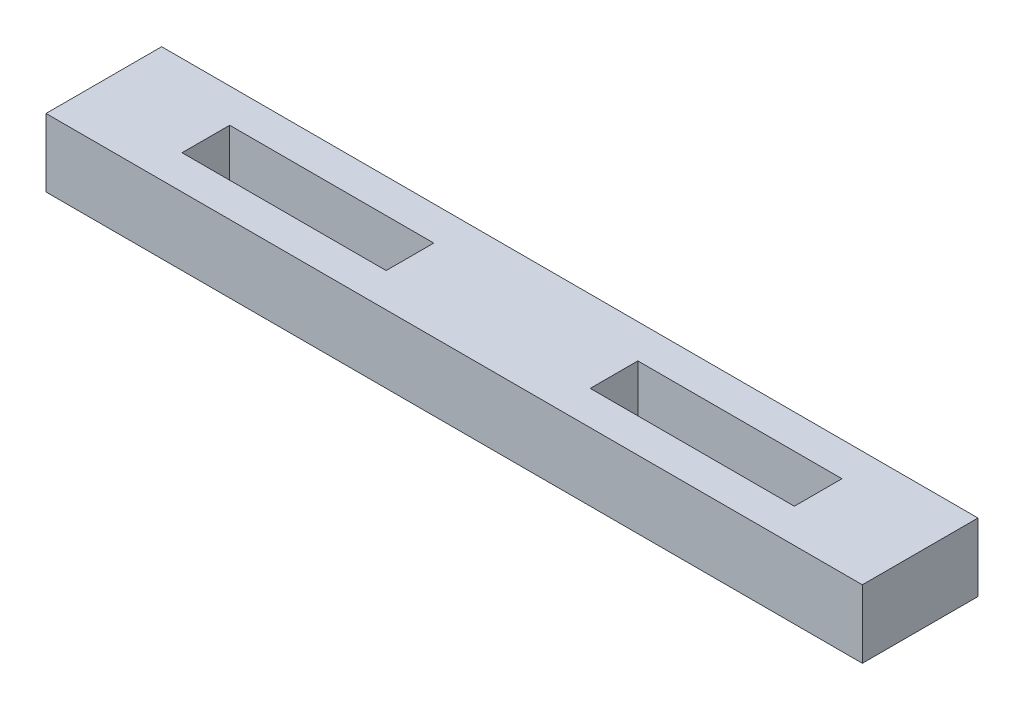
SolidWorks part; units mm, degrees
other "Markup1"
sketch "Sketch3" plane through (152.4, 12.7, 0) normal (0.061, 0.9981, 0.0037) x (-0.0466, 0.0065, -0.9989)
ref_plane "Front Plane" through (0, 0, 0) normal (0, 0, 1) x (1, 0, 0)
ref_plane "Top Plane" through (0, 0, 0) normal (0, 1, 0) x (1, 0, 0)
ref_plane "Right Plane" through (0, 0, 0) normal (1, 0, 0) x (0, 0, -1)
sketch "Sketch1" plane through (0, 0, 0) normal (0, 1, 0) x (1, 0, 0)
  line L1 (0, 0) -> (152.4, 0)
  line L2 (0, 0) -> (0, 21.59)
  line L3 (0, 21.59) -> (152.4, 21.59)
  line L4 (152.4, 0) -> (152.4, 21.59)
  dimension "D1" = 152.4
  dimension "D2" = 21.59
extrude "Boss-Extrude1" add sketch "Sketch1" along normal blind 12.7
sketch "Sketch2" plane through (0, 12.7, 0) normal (0, 1, 0) x (1, 0, 0)
  line L0 (0, 0) -> (152.4, 0) construction
  line L1 (19.05, 6.35) -> (57.15, 6.35)
  line L2 (19.05, 6.35) -> (19.05, 15.24)
  line L3 (19.05, 15.24) -> (57.15, 15.24)
  line L4 (57.15, 6.35) -> (57.15, 15.24)
  line L5 (95.25, 15.24) -> (133.35, 15.24)
  line L6 (95.25, 15.24) -> (95.25, 6.35)
  line L7 (95.25, 6.35) -> (133.35, 6.35)
  line L8 (133.35, 15.24) -> (133.35, 6.35)
  line L10 (0, 21.59) -> (0, 0) construction
  line L11 (152.4, 0) -> (152.4, 21.59) construction
  dimension "D1" = 38.1
  dimension "D2" = 38.1
  dimension "D3" = 8.89
  dimension "D4" = 8.89
  dimension "D5" = 6.35
  dimension "D6" = 19.05
  dimension "D7" = 19.05
  dimension "D8" = 6.35
extrude "Cut-Extrude1" cut sketch "Sketch2" against normal through all both and the other way through all
